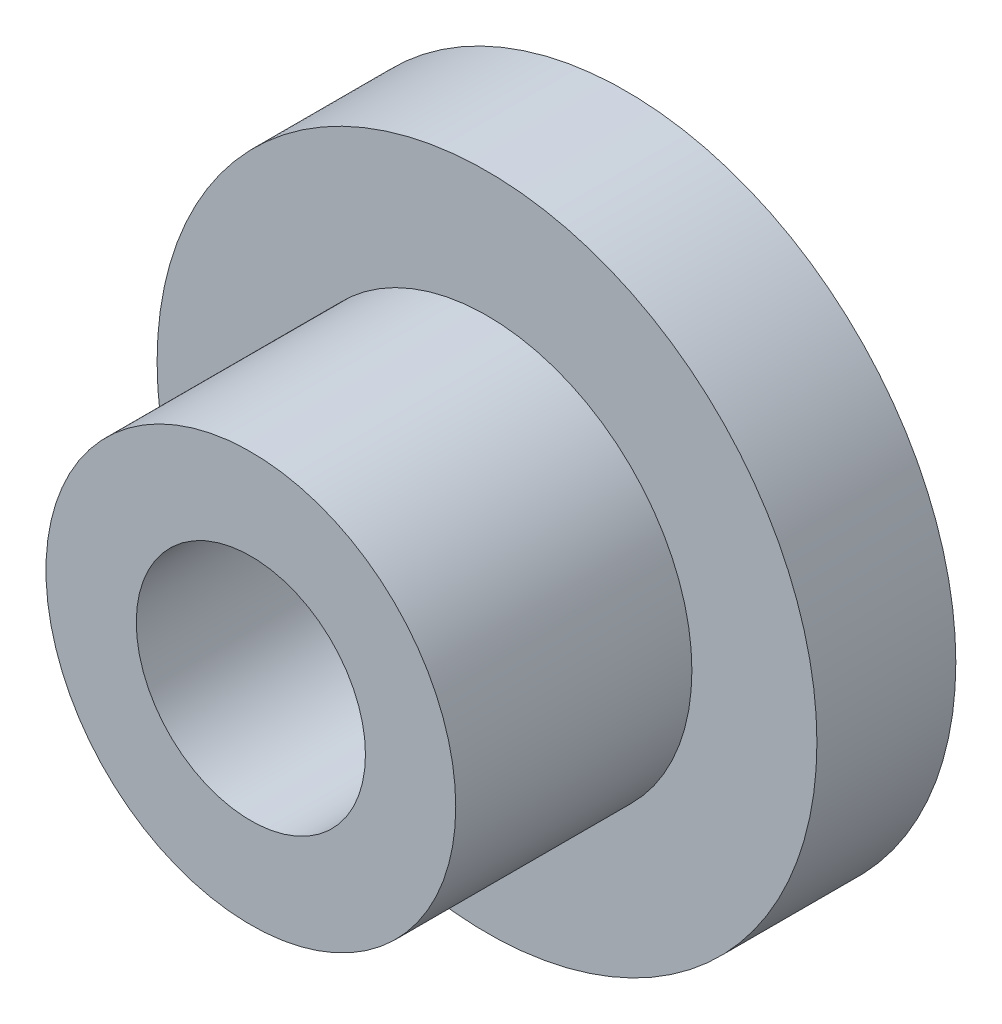
SolidWorks part; units mm, degrees
material "6061-T6 (SS)"
ref_plane "Front Plane" through (0, 0, 0) normal (0, 0, 1) x (1, 0, 0)
ref_plane "Top Plane" through (0, 0, 0) normal (0, 1, 0) x (1, 0, 0)
ref_plane "Right Plane" through (0, 0, 0) normal (1, 0, 0) x (0, 0, -1)
sketch "Sketch1" plane through (0, 0, 0) normal (1, 0, 0) x (0, 0, -1)
  line L0 (-90.1443, 0) -> (-71.7076, 0) construction
  line L1 (0, 0) -> (0, 4.75)
  line L2 (0, 4.75) -> (-2, 4.75)
  line L3 (-2, 4.75) -> (-2, 2.95)
  line L4 (-2, 2.95) -> (-5.4, 2.95)
  line L5 (-5.4, 2.95) -> (-5.4, 0)
  line L8 (-5.4, 0) -> (0, 0)
  dimension "D1" = 9.5
  dimension "D2" = 5.9
  dimension "D3" = 2
  dimension "D4" = 5.4
revolve "Revolve1" add sketch "Sketch1" angle 360 about L0
hole_wizard "M4x0.7 Tapped Hole1" positions "Sketch3" profile "Sketch2" tap size "M4x0.7" standard "ANSI Metric" end condition up to next
sketch "Sketch3" plane through (-1.5852, 0.8827, 5.4) normal (0, 0, 1) x (1, 0, 0)
  point P0 (1.5852, -0.8827)
sketch "Sketch2" plane through (0, 0, 5.4) normal (1, 0, 0) x (0, -1, 0)
  line L0 (0, 0) -> (0, 5.4)
  line L1 (0, 5.4) -> (1.65, 5.4)
  line L2 (1.65, 5.4) -> (1.65, 0)
  line L5 (1.65, 0) -> (0, 0)
  line L11 (0, -6.35) -> (0, 107.95) construction
  dimension "Thru Tap Drill Dia." = 3.3
  dimension "Thru Tap Drill Depth" = 5.4
cosmetic thread "Hole Thread2"
